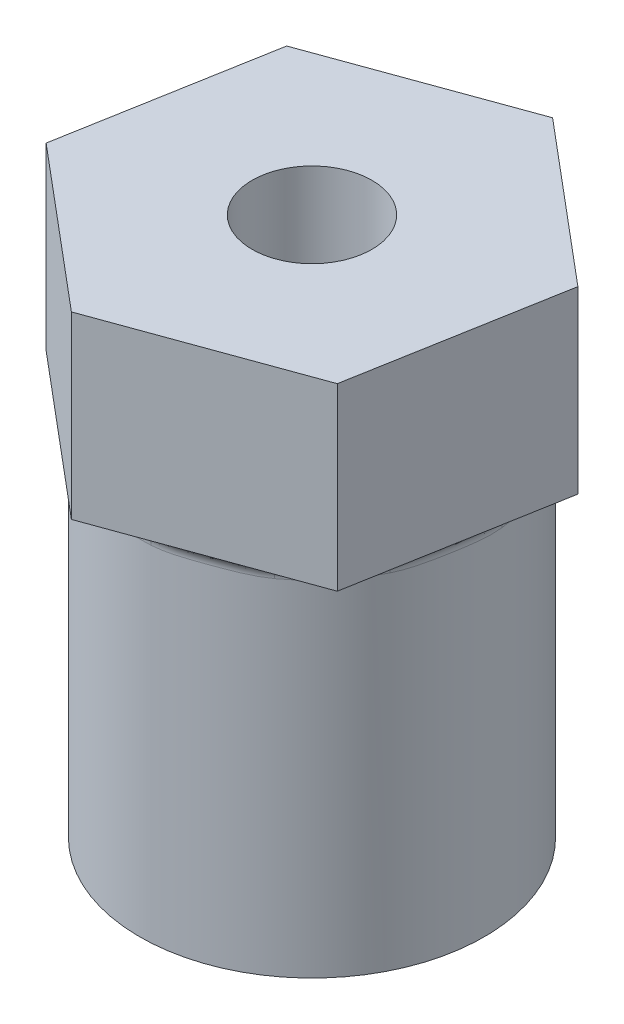
SolidWorks part; units mm, degrees
ref_plane "Front Plane" through (0, 0, 0) normal (0, 0, 1) x (1, 0, 0)
ref_plane "Top Plane" through (0, 0, 0) normal (0, 1, 0) x (1, 0, 0)
ref_plane "Right Plane" through (0, 0, 0) normal (1, 0, 0) x (0, 0, -1)
sketch "Sketch1" plane through (0, 0, 0) normal (0, 1, 0) x (1, 0, 0)
  line L1 (1.2098, 6.8218) -> (-5.3029, 4.4586)
  line L2 (-5.3029, 4.4586) -> (-6.5127, -2.3632)
  line L3 (-6.5127, -2.3632) -> (-1.2098, -6.8218)
  line L4 (-1.2098, -6.8218) -> (5.3029, -4.4586)
  line L5 (5.3029, -4.4586) -> (6.5127, 2.3632)
  line L6 (6.5127, 2.3632) -> (1.2098, 6.8218)
  circle A0 centre (0, 0) radius 6 construction
  point P1 (3.8612, 4.5925)
  dimension "D1" = 12
extrude "Boss-Extrude1" add sketch "Sketch1" along normal blind 6
sketch "Sketch2" plane through (0, 0, 0) normal (0, -1, 0) x (-1, 0, 0)
  circle A0 centre (0, 0) radius 5.75
  dimension "D1" = 11.5
extrude "Boss-Extrude2" add sketch "Sketch2" along normal blind 12
fillet "Fillet1" radius 0.5 1 edges at (0, 0, -5.75)
sketch "Sketch3" plane through (0, -12, 0) normal (0, -1, 0) x (-1, 0, 0)
  circle A0 centre (0, 0) radius 2
  dimension "D1" = 4
extrude "Cut-Extrude1" cut sketch "Sketch3" against normal through all
